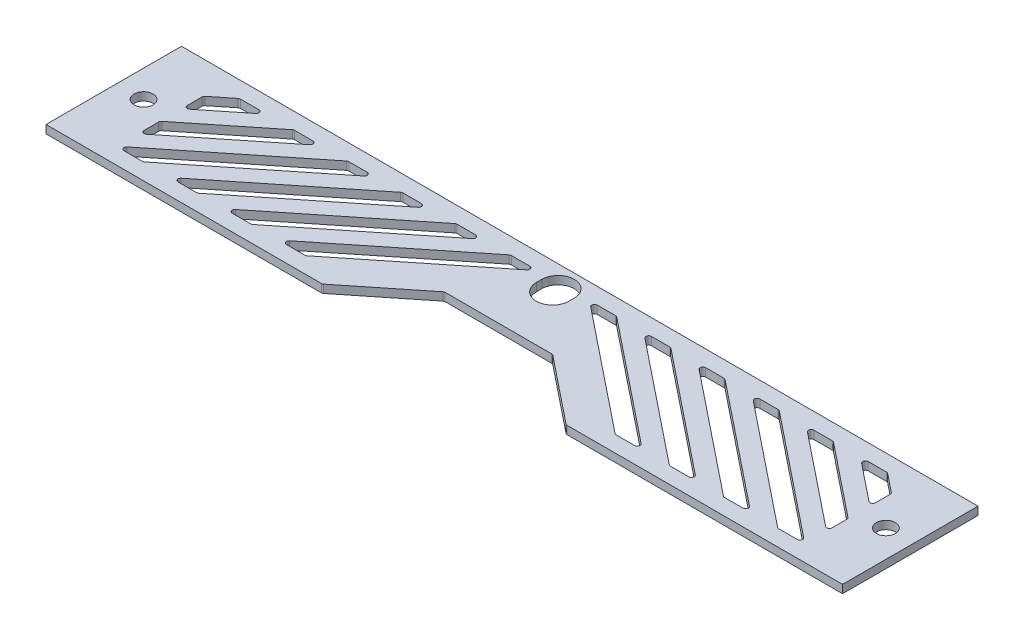
SolidWorks part; units mm, degrees
ref_plane "前视基准面" through (0, 0, 0) normal (0, 0, 1) x (1, 0, 0)
ref_plane "上视基准面" through (0, 0, 0) normal (0, 1, 0) x (1, 0, 0)
ref_plane "右视基准面" through (0, 0, 0) normal (1, 0, 0) x (0, 0, -1)
sketch "草图1" plane through (0, 0, 0) normal (0, 1, 0) x (1, 0, 0)
  line L1 (-73.5, 12.5) -> (73.5, 12.5)
  line L2 (-73.5, 12.5) -> (-73.5, -12.5)
  line L3 (-73.5, -12.5) -> (73.5, -12.5)
  line L4 (73.5, 12.5) -> (73.5, -12.5)
  line L5 (-73.5, 12.5) -> (73.5, -12.5) construction
  line L6 (-73.5, -12.5) -> (73.5, 12.5) construction
  point P0 (0, 0)
  dimension "D1" = 147
  dimension "D2" = 25
extrude "凸台-拉伸1" add sketch "草图1" along normal blind 1.5
sketch "草图2" plane through (0, 0, 0) normal (0, -1, 0) x (1, 0, 0)
  line L0 (10, 2.5) -> (-10, 2.5)
  line L1 (-10, 2.5) -> (-22.5, 12.5)
  line L2 (-73.5, 12.5) -> (73.5, 12.5) construction
  line L3 (-22.5, 12.5) -> (22.5, 12.5)
  line L4 (22.5, 12.5) -> (10, 2.5)
  point P5 (0, 2.5)
  point P7 (0, 12.5)
  dimension "D1" = 10
  dimension "D2" = 20
  dimension "D3" = 45
extrude "切除-拉伸1" cut sketch "草图2" against normal through all
sketch "草图3" plane through (0, 0, 0) normal (0, -1, 0) x (1, 0, 0)
  line L0 (-16.0523, -0.5) -> (-28.5523, 9.5)
  line L1 (-21.0523, -0.5) -> (-33.5523, 9.5)
  line L2 (-26.0523, -0.5) -> (-38.5523, 9.5)
  line L3 (-31.0523, -0.5) -> (-43.5523, 9.5)
  line L4 (-36.0523, -0.5) -> (-48.5523, 9.5)
  line L5 (-41.0523, -0.5) -> (-53.5523, 9.5)
  line L6 (-46.0523, -0.5) -> (-58.5523, 9.5)
  line L7 (-51.0523, -0.5) -> (-63.5523, 9.5)
  line L8 (0, -0.5) -> (0, -9.5)
  line L9 (-56.0523, -0.5) -> (-68.5523, 9.5)
  line L10 (-61.0523, -0.5) -> (-70.5, 7.0581)
  line L11 (-66.0523, -0.5) -> (-70.5, 3.0581)
  line L15 (-16.0523, -0.5) -> (-4.8023, -9.5)
  line L16 (70.5, 9.5) -> (23.5523, 9.5)
  line L17 (23.5523, 9.5) -> (11.0523, -0.5)
  line L18 (11.0523, -0.5) -> (-11.0523, -0.5)
  line L19 (-11.0523, -0.5) -> (-23.5523, 9.5)
  line L20 (-23.5523, 9.5) -> (-70.5, 9.5)
  line L21 (-70.5, 9.5) -> (-70.5, -9.5)
  line L22 (-70.5, -9.5) -> (70.5, -9.5)
  line L23 (70.5, -9.5) -> (70.5, 9.5)
  line L26 (0, -0.5) -> (-11.0523, -0.5)
  line L27 (-11.0523, -0.5) -> (-23.5523, 9.5)
  line L28 (-23.5523, 9.5) -> (-70.5, 9.5)
  line L29 (-70.5, 9.5) -> (-70.5, -9.5)
  line L30 (-70.5, -9.5) -> (0, -9.5)
  line L32 (-21.0523, -0.5) -> (-9.8023, -9.5)
  line L33 (-26.0523, -0.5) -> (-14.8023, -9.5)
  line L34 (-31.0523, -0.5) -> (-19.8023, -9.5)
  line L35 (-36.0523, -0.5) -> (-24.8023, -9.5)
  line L36 (-41.0523, -0.5) -> (-29.8023, -9.5)
  line L37 (-46.0523, -0.5) -> (-34.8023, -9.5)
  line L38 (-51.0523, -0.5) -> (-39.8023, -9.5)
  line L39 (-56.0523, -0.5) -> (-44.8023, -9.5)
  line L41 (-61.0523, -0.5) -> (-49.8023, -9.5)
  line L42 (-66.0523, -0.5) -> (-54.8023, -9.5)
  line L43 (-70.5, -0.9419) -> (-59.8023, -9.5)
  line L44 (-70.5, -4.9419) -> (-64.8023, -9.5)
  line L46 (-71.0523, -0.5) -> (-83.5523, 9.5) [skipped]
  line L47 (-76.0523, -0.5) -> (-88.5523, 9.5) [skipped]
  line L48 (-81.0523, -0.5) -> (-93.5523, 9.5) [skipped]
  dimension "D2" = 15
  dimension "D3" = 78.3023
  dimension "D1" = 3
extrude "切除-拉伸2" cut sketch "草图3" against normal blind 10 contours L1 L32 L30 L15 L0 L28 | L3 L34 L30 L33 L2 L28 | L5 L36 L30 L35 L4 L28 | L7 L38 L30 L37 L6 L28 | L10 L41 L30 L39 L9 L28 L29 | L29 L43 L30 L42 L11 | L44 L29 L30
mirror "镜向3" about plane through (0, 0, 0) normal (1, 0, 0) of "切除-拉伸2"
fillet "圆角2" radius 0.5 64 edges at (59.8023, 0.75, -9.5) (54.8023, 0.75, -9.5) (70.5, 0.75, 3.0581) (70.5, 0.75, -0.9419) (-58.5523, 0.75, 9.5) (-34.8023, 0.75, -9.5) (-39.8023, 0.75, -9.5) (-63.5523, 0.75, 9.5) (-70.5, 0.75, 9.5) (-68.5523, 0.75, 9.5) (-44.8023, 0.75, -9.5) (-49.8023, 0.75, -9.5) (-70.5, 0.75, 7.0581) (-38.5523, 0.75, 9.5) (-14.8023, 0.75, -9.5) (-19.8023, 0.75, -9.5) (-43.5523, 0.75, 9.5) (-48.5523, 0.75, 9.5) (-24.8023, 0.75, -9.5) (-29.8023, 0.75, -9.5) (-53.5523, 0.75, 9.5) (-70.5, 0.75, -9.5) (-70.5, 0.75, -4.9419) (-64.8023, 0.75, -9.5) (-28.5523, 0.75, 9.5) (-9.8023, 0.75, -9.5) (-33.5523, 0.75, 9.5) (10, 0.75, 2.5) (-10, 0.75, 2.5) (-22.5, 0.75, 12.5) (-73.5, 0.75, 12.5) (-73.5, 0.75, -12.5) (73.5, 0.75, -12.5) (73.5, 0.75, 12.5) (22.5, 0.75, 12.5) (-70.5, 0.75, 3.0581) (-54.8023, 0.75, -9.5) (-59.8023, 0.75, -9.5) (-70.5, 0.75, -0.9419) (34.8023, 0.75, -9.5) (39.8023, 0.75, -9.5) (44.8023, 0.75, -9.5) (49.8023, 0.75, -9.5) (14.8023, 0.75, -9.5) (19.8023, 0.75, -9.5) (24.8023, 0.75, -9.5) (29.8023, 0.75, -9.5) (64.8023, 0.75, -9.5) (70.5, 0.75, -9.5) (4.8023, 0.75, -9.5) (9.8023, 0.75, -9.5) (28.5523, 0.75, 9.5) (63.5523, 0.75, 9.5) (58.5523, 0.75, 9.5) (70.5, 0.75, 9.5) (68.5523, 0.75, 9.5) (43.5523, 0.75, 9.5) (38.5523, 0.75, 9.5) (53.5523, 0.75, 9.5) (48.5523, 0.75, 9.5) (33.5523, 0.75, 9.5) (70.5, 0.75, -4.9419) (70.5, 0.75, 7.0581) (-4.8023, 0.75, -9.5)
sketch "草图4" plane through (0, 1.5, 0) normal (0, 1, 0) x (1, 0, 0)
  line L0 (73, 12.5) -> (-73, 12.5) construction
  line L1 (73.5, -12.5) -> (63.5, -12.5)
  line L2 (73.5, -12.5) -> (73.5, 12.5)
  line L3 (73.5, 12.5) -> (63.5, 12.5)
  line L4 (63.5, -12.5) -> (63.5, 12.5)
  line L5 (73.5, -12) -> (73.5, 12) construction
  dimension "D1" = 10
  dimension "D2" = 25
extrude "凸台-拉伸2" add sketch "草图4" against normal up to surface (1.5 mm away) up to face at (49.1773, 0, 0)
mirror "镜向4" about plane through (0, 0, 0) normal (1, 0, 0) of "凸台-拉伸2"
fillet "圆角3" radius 0.5 8 edges at (63.5, 0.75, -6.5419) (63.5, 0.75, -2.5419) (63.5, 0.75, 1.4581) (63.5, 0.75, 5.4581) (-63.5, 0.75, -6.5419) (-63.5, 0.75, -2.5419) (-63.5, 0.75, 1.4581) (-63.5, 0.75, 5.4581)
sketch "草图5" plane through (0, 0, 0) normal (0, -1, 0) x (1, 0, 0)
  line L0 (73.5, -12.5) -> (-73.5, -12.5) construction
  line L1 (-73.5, -12.5) -> (-73.5, 12.5) construction
  line L2 (73.5, 12.5) -> (73.5, -12.5) construction
  circle A0 centre (-68.5, -0.5) radius 1.75
  circle A1 centre (68.5, -0.5) radius 1.75
  dimension "D2" = 5
  dimension "D4" = 5
  dimension "D5" = 3.5
  dimension "D1" = 12
  dimension "D3" = 12
extrude "切除-拉伸3" cut sketch "草图5" against normal through all
sketch "草图6" plane through (0, 1.5, 0) normal (0, 1, 0) x (1, 0, 0)
  line L0 (0, 8.5) -> (0, 7.5) construction
  line L1 (3, 8.5) -> (3, 7.5)
  line L2 (-3, 8.5) -> (-3, 7.5)
  arc A0 (3, 8.5) -> (-3, 8.5) centre (0, 8.5) ccw
  arc A1 (-3, 7.5) -> (3, 7.5) centre (0, 7.5) ccw
  point P3 (0, 8)
  dimension "D3" = 3
  dimension "D1" = 8
  dimension "D2" = 1
extrude "切除-拉伸4" cut sketch "草图6" against normal through all
